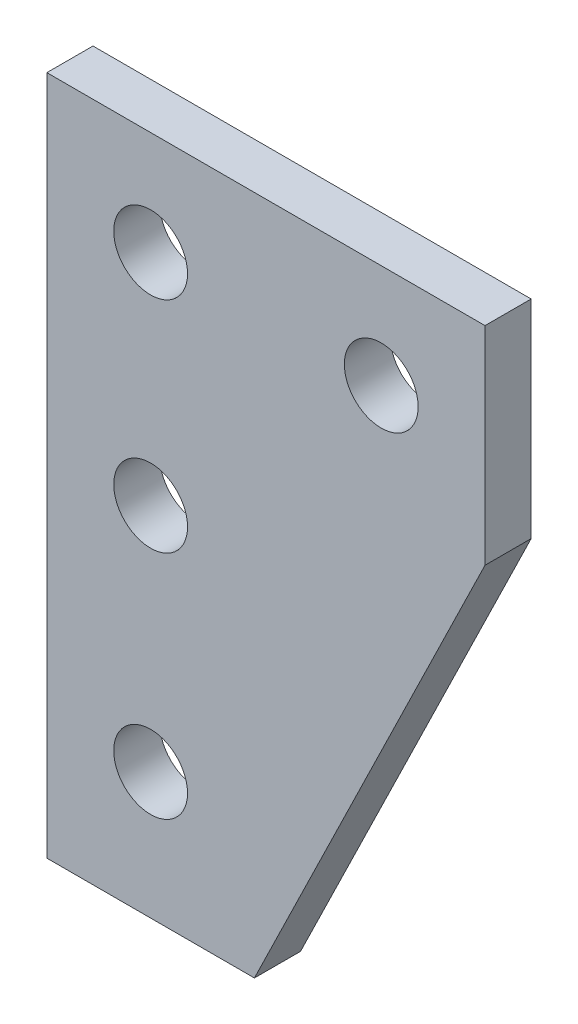
SolidWorks part; units mm, degrees
ref_plane "正面" through (0, 0, 0) normal (0, 0, 1) x (1, 0, 0)
ref_plane "平面" through (0, 0, 0) normal (0, 1, 0) x (1, 0, 0)
ref_plane "右側面" through (0, 0, 0) normal (1, 0, 0) x (0, 0, -1)
sketch "ｽｹｯﾁ1" plane through (0, 0, 0) normal (0, 0, 1) x (1, 0, 0)
  line L1 (-25, 25) -> (25, 25)
  line L2 (-25, 25) -> (-25, -25)
  line L3 (-25, -25) -> (25, -25)
  line L4 (25, 25) -> (25, -25)
  line L5 (-25, 25) -> (25, -25) construction
  line L6 (-25, -25) -> (25, 25) construction
  point P0 (0, 0)
  dimension "D1" = 50
  dimension "D2" = 50
extrude "ﾎﾞｽ - 押し出し1" add sketch "ｽｹｯﾁ1" along normal blind 2
sketch "ｽｹｯﾁ2" plane through (0, 0, 2) normal (0, 0, 1) x (1, 0, 0)
  line L0 (0, 0) -> (0, -9.51)
  line L1 (0, -9.51) -> (0, -19.51)
  line L2 (0, 0) -> (10, 0)
  circle A0 centre (0, 0) radius 1.6
  circle A1 centre (0, -9.51) radius 1.6
  circle A2 centre (0, -19.51) radius 1.6
  circle A3 centre (10, 0) radius 1.6
  dimension "D4" = 3.2
  dimension "D5" = 3.2
  dimension "D6" = 3.2
  dimension "D7" = 3.2
  dimension "D1" = 9.51
  dimension "D2" = 10
  dimension "D3" = 10
extrude "ｶｯﾄ - 押し出し1" cut sketch "ｽｹｯﾁ2" against normal blind 10
sketch "ｽｹｯﾁ3" plane through (0, 0, 2) normal (0, 0, 1) x (1, 0, 0)
  line L0 (14.5, -4.5) -> (4.5, -25)
  line L2 (-4.5, 4.5) -> (-4.5, -25)
  line L3 (-25, -25) -> (25, -25) construction
  line L4 (-39.2263, 35.2493) -> (37.3228, 35.2493)
  line L6 (4.5, -25) -> (-4.5, -25)
  line L7 (-39.2263, 35.2493) -> (-39.2263, -28.247)
  line L8 (-39.2263, -28.247) -> (37.3228, -28.247)
  line L9 (37.3228, 35.2493) -> (37.3228, -28.247)
  line L11 (-39.2263, 35.2493) -> (37.3228, -28.247) construction
  line L13 (-4.5, 4.5) -> (14.5, 4.5)
  line L14 (14.5, 4.5) -> (14.5, -4.5)
  line L15 (-39.2263, -28.247) -> (37.3228, 35.2493) construction
  point P0 (-0.9518, 3.5011)
extrude "ｶｯﾄ - 押し出し3" cut sketch "ｽｹｯﾁ3" against normal blind 10
